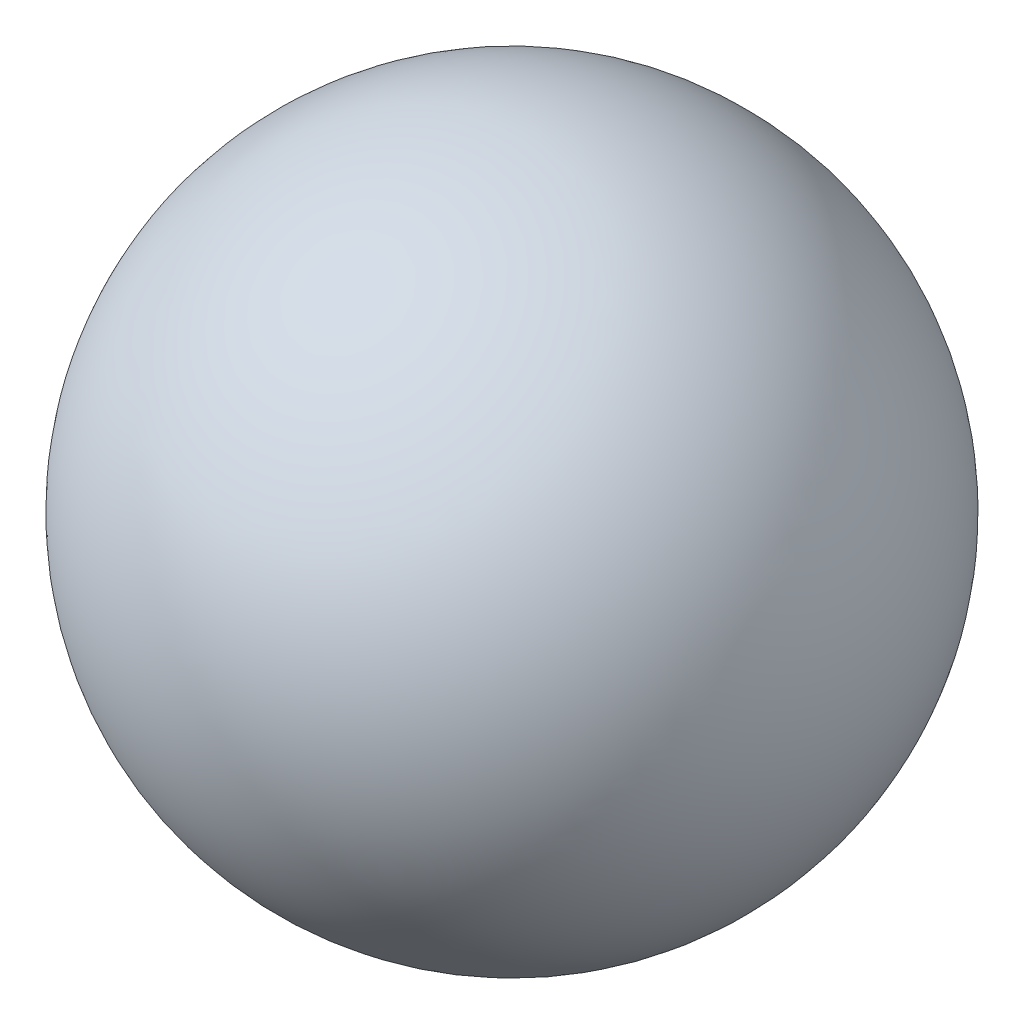
SolidWorks part; units mm, degrees
ref_plane "Front Plane" through (0, 0, 0) normal (0, 0, 1) x (1, 0, 0)
ref_plane "Top Plane" through (0, 0, 0) normal (0, 1, 0) x (1, 0, 0)
ref_plane "Right Plane" through (0, 0, 0) normal (1, 0, 0) x (0, 0, -1)
sketch "Sketch1" plane through (0, 0, 0) normal (0, 0, 1) x (1, 0, 0)
  line L0 (-44.45, 0) -> (44.45, 0)
  arc A0 (44.45, 0) -> (-44.45, 0) centre (0, 0) ccw
  dimension "D1" = 88.9
revolve "Revolve1" add sketch "Sketch1" angle 360 about L0
ref_plane "Plane1" through (0, 0, 44.45) normal (0, 0, 1) x (1, 0, 0)
sketch "Sketch2" plane through (0, 0, 44.45) normal (0, 0, 1) x (1, 0, 0)
  line L0 (0, 5.852) -> (0, -5.852) construction
  line L1 (5.852, 0) -> (-5.852, 0) construction
  line L2 (-0.6, 5.852) -> (-0.6, 0.6)
  line L3 (5.852, 0.6) -> (0.6, 0.6)
  line L4 (0.6, 5.852) -> (0.6, 0.6)
  line L5 (5.852, -0.6) -> (0.6, -0.6)
  line L6 (-0.6, 5.852) -> (0.6, 5.852)
  line L7 (-0.6, -5.852) -> (0.6, -5.852)
  line L8 (5.852, 0.6) -> (5.852, -0.6)
  line L9 (-5.852, 0.6) -> (-5.852, -0.6)
  line L10 (-0.6, 0.6) -> (-5.852, 0.6)
  line L11 (-0.6, -0.6) -> (-5.852, -0.6)
  line L12 (5.852, 0.6) -> (-5.852, 0.6) construction
  line L13 (-0.6, -0.6) -> (-0.6, -5.852)
  line L14 (5.852, -0.6) -> (-5.852, -0.6) construction
  line L15 (0.6, -0.6) -> (0.6, -5.852)
  line L16 (-0.6, 5.852) -> (-0.6, -5.852) construction
  line L17 (-0.6, 29.2598) -> (-0.6, 24.0078)
  line L18 (0.6, 5.852) -> (0.6, -5.852) construction
  line L19 (5.852, 24.0078) -> (0.6, 24.0078)
  line L20 (0.6, 29.2598) -> (0.6, 24.0078)
  line L21 (5.852, 22.8078) -> (0.6, 22.8078)
  line L22 (-0.6, 29.2598) -> (0.6, 29.2598)
  line L23 (-0.6, 17.5559) -> (0.6, 17.5559)
  line L24 (5.852, 24.0078) -> (5.852, 22.8078)
  line L25 (-5.852, 24.0078) -> (-5.852, 22.8078)
  line L26 (-0.6, 24.0078) -> (-5.852, 24.0078)
  line L27 (-0.6, 22.8078) -> (-5.852, 22.8078)
  line L28 (-0.6, 22.8078) -> (-0.6, 17.5559)
  line L29 (0.6, 22.8078) -> (0.6, 17.5559)
  line L30 (0, 29.2598) -> (0, 17.5559) construction
  line L31 (5.852, 23.4078) -> (-5.852, 23.4078) construction
  line L32 (-0.6, 52.6676) -> (-0.6, 47.4156)
  line L33 (5.852, 47.4156) -> (0.6, 47.4156)
  line L34 (0.6, 52.6676) -> (0.6, 47.4156)
  line L35 (5.852, 46.2156) -> (0.6, 46.2156)
  line L36 (-0.6, 52.6676) -> (0.6, 52.6676)
  line L37 (-0.6, 40.9637) -> (0.6, 40.9637)
  line L38 (5.852, 47.4156) -> (5.852, 46.2156)
  line L39 (-5.852, 47.4156) -> (-5.852, 46.2156)
  line L40 (-0.6, 47.4156) -> (-5.852, 47.4156)
  line L41 (-0.6, 46.2156) -> (-5.852, 46.2156)
  line L42 (-0.6, 46.2156) -> (-0.6, 40.9637)
  line L43 (0.6, 46.2156) -> (0.6, 40.9637)
  line L44 (0, 52.6676) -> (0, 40.9637) construction
  line L45 (5.852, 46.8156) -> (-5.852, 46.8156) construction
  line L46 (0, 0) -> (0, 23.4078) construction
  point P3 (0, 0)
  point P8 (0, 0)
  point P24 (0, 23.4078)
  point P28 (0, 23.4078)
  point P42 (0, 46.8156)
  point P46 (0, 46.8156)
  dimension "D1" = 11.7039
  dimension "D5" = 23.4078
  dimension "D2" = 0.6
  dimension "D3" = 0.6
  dimension "D4" = 3
